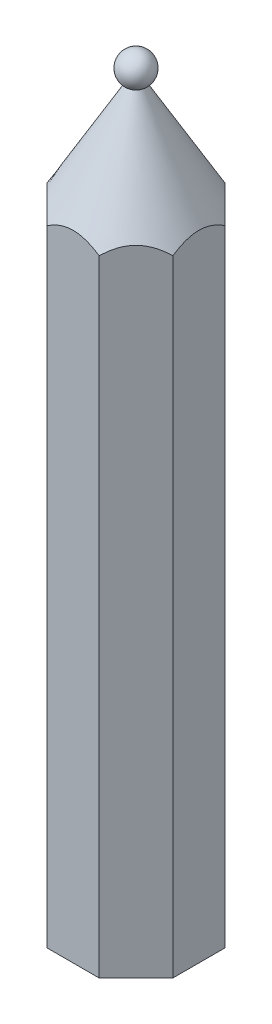
SolidWorks part; units mm, degrees
ref_plane "Front Plane" through (0, 0, 0) normal (0, 0, 1) x (1, 0, 0)
ref_plane "Top Plane" through (0, 0, 0) normal (0, 1, 0) x (1, 0, 0)
ref_plane "Right Plane" through (0, 0, 0) normal (1, 0, 0) x (0, 0, -1)
sketch "Sketch1" plane through (0, 0, 0) normal (0, 1, 0) x (1, 0, 0)
  line L0 (-12.0711, -5) -> (-12.0711, 5)
  line L1 (-12.0711, 5) -> (-5, 12.0711)
  line L2 (-5, 12.0711) -> (5, 12.0711)
  line L3 (5, 12.0711) -> (12.0711, 5)
  line L4 (12.0711, 5) -> (12.0711, -5)
  line L5 (12.0711, -5) -> (5, -12.0711)
  line L6 (5, -12.0711) -> (-5, -12.0711)
  line L7 (-5, -12.0711) -> (-12.0711, -5)
  point P10 (-12.0711, 0)
  point P12 (0, -12.0711)
  dimension "D1" = 10
extrude "Boss-Extrude1" add sketch "Sketch1" along normal blind 140
sketch "Sketch3" plane through (0, 0, 0) normal (0, 0, 1) x (1, 0, 0)
  line L0 (1.5, 140) -> (14.4227, 117.6173)
  line L1 (-5, 140) -> (5, 140) construction
  line L3 (14.4227, 117.6173) -> (14.4227, 140)
  line L4 (14.4227, 140) -> (1.5, 140)
  line L5 (0, 140) -> (0, 128.9175) construction
  point P6 (0, 140)
  dimension "D1" = 1.5
  dimension "D2" = 60
revolve "Cut-Revolve2" cut sketch "Sketch3" angle 360 about L5
sketch "Sketch4" plane through (0, 0, 0) normal (0, 0, 1) x (1, 0, 0)
  line L0 (0, 145.5981) -> (0, 140)
  line L1 (1.5, 140) -> (-1.5, 140) construction
  line L2 (0, 140) -> (1.5, 140)
  arc A0 (1.5, 140) -> (0, 145.5981) centre (0, 142.5981) ccw
  dimension "D1" = 3
revolve "Revolve1" add sketch "Sketch4" angle 360 about L0
sketch "Sketch5" plane through (0, 0, 0) normal (0, 0, 1) x (1, 0, 0)
  line L0 (0, 0) -> (5, 0)
  line L1 (5, 0) -> (12.0711, 0) construction
  line L2 (5, 0) -> (5, 110)
  line L3 (5, 119.9677) -> (5, 0) construction
  line L4 (5, 110) -> (0, 118.6603)
  line L5 (0, 118.6603) -> (0, 0)
  point P5 (5, 0)
  dimension "D1" = 5
  dimension "D2" = 110
  dimension "D3" = 150
revolve "Cut-Revolve3" cut sketch "Sketch5" angle 360 about L5
